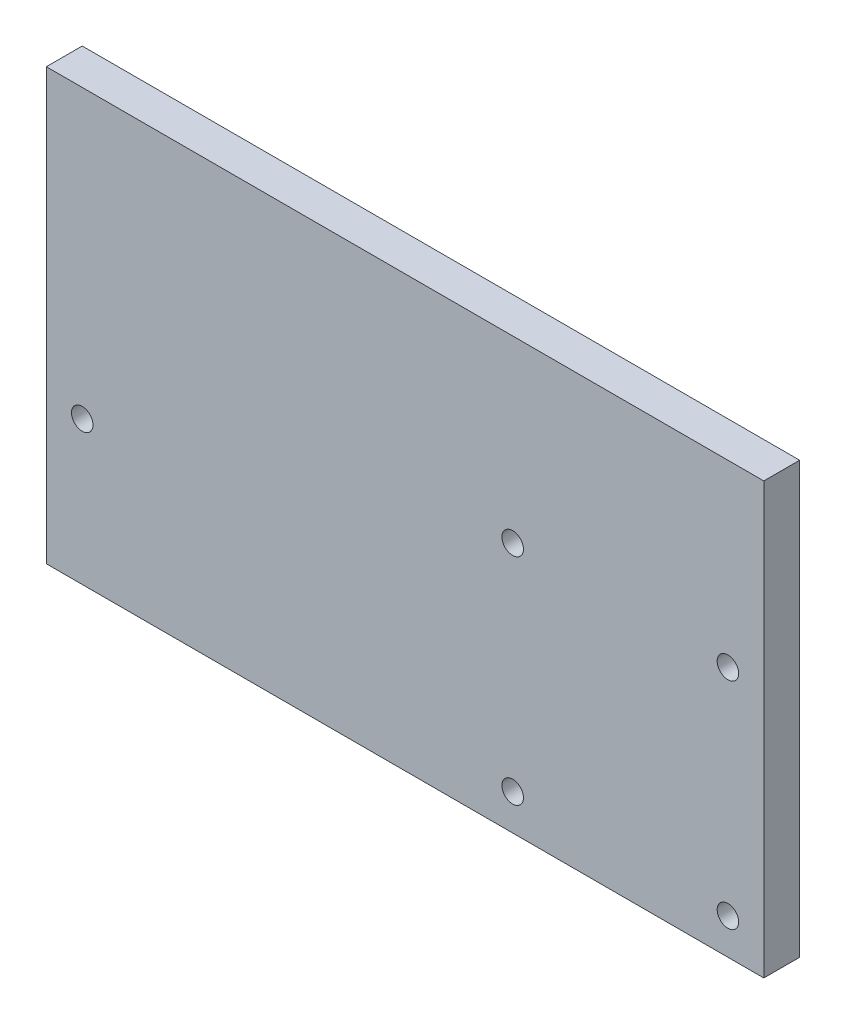
SolidWorks part; units mm, degrees
ref_plane "Front Plane" through (0, 0, 0) normal (0, 0, 1) x (1, 0, 0)
ref_plane "Top Plane" through (0, 0, 0) normal (0, 1, 0) x (1, 0, 0)
ref_plane "Right Plane" through (0, 0, 0) normal (1, 0, 0) x (0, 0, -1)
sketch "Sketch1" plane through (0, 0, 0) normal (0, 0, 1) x (1, 0, 0)
  line L1 (0, 0) -> (127, 0)
  line L2 (0, 0) -> (0, -76.2)
  line L3 (0, -76.2) -> (127, -76.2)
  line L4 (127, 0) -> (127, -76.2)
  dimension "D2" = 76.2
  dimension "D3" = 127
extrude "Boss-Extrude1" add sketch "Sketch1" along normal blind 6.35
sketch "Sketch2" plane through (0, 0, 6.35) normal (0, 0, 1) x (1, 0, 0)
  line L0 (127, -76.2) -> (127, 0) construction
  line L1 (82.55, -31.75) -> (120.65, -31.75) construction
  line L2 (82.55, -31.75) -> (82.55, -69.85) construction
  line L3 (82.55, -69.85) -> (120.65, -69.85) construction
  line L4 (120.65, -31.75) -> (120.65, -69.85) construction
  line L5 (0, -76.2) -> (127, -76.2) construction
  line L6 (0, 0) -> (0, -76.2) construction
  circle A0 centre (82.55, -31.75) radius 1.905
  circle A1 centre (120.65, -31.75) radius 1.905
  circle A2 centre (82.55, -69.85) radius 1.905
  circle A3 centre (120.65, -69.85) radius 1.905
  circle A4 centre (6.35, -50.8) radius 1.905
  point P14 (82.55, -50.8)
  dimension "D4" = 3.81
  dimension "D6" = 3.81
  dimension "D1" = 6.35
  dimension "D2" = 6.35
  dimension "D3" = 38.1
  dimension "D5" = 6.35
extrude "Cut-Extrude1" cut sketch "Sketch2" against normal up to next
